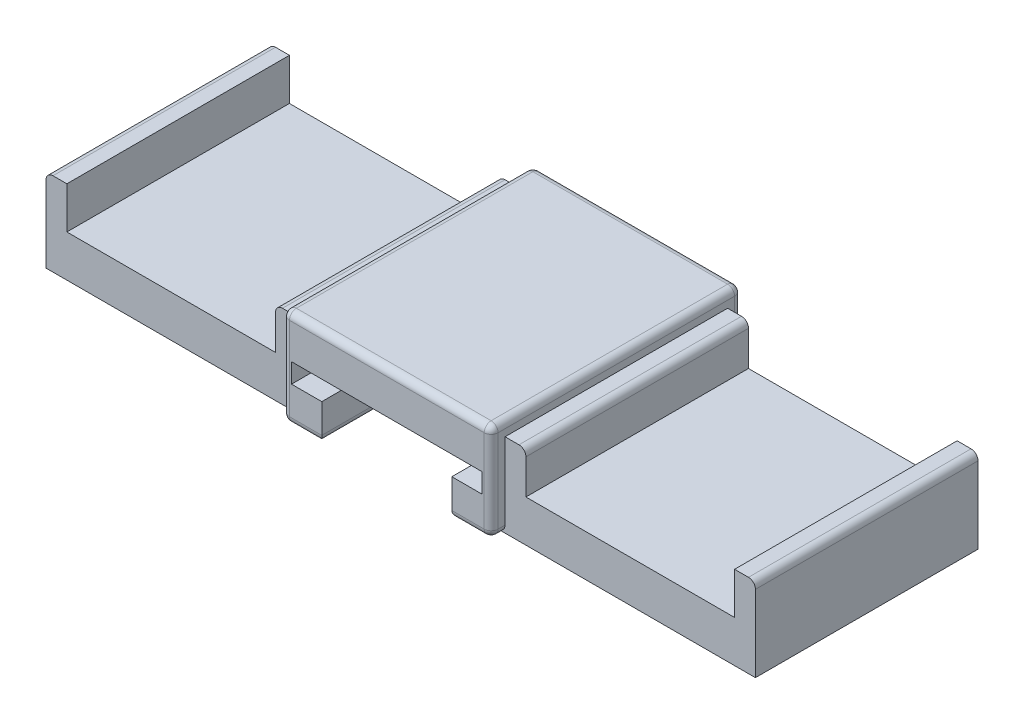
SolidWorks part; units mm, degrees
ref_plane "Front Plane" through (0, 0, 0) normal (0, 0, 1) x (1, 0, 0)
ref_plane "Top Plane" through (0, 0, 0) normal (0, 1, 0) x (1, 0, 0)
ref_plane "Right Plane" through (0, 0, 0) normal (1, 0, 0) x (0, 0, -1)
sketch "Sketch1" plane through (0, 0, 0) normal (0, 1, 0) x (1, 0, 0)
  line L1 (-7.5, -9) -> (7.5, -9)
  line L2 (-7.5, -9) -> (-7.5, 9)
  line L3 (-7.5, 9) -> (7.5, 9)
  line L4 (7.5, -9) -> (7.5, 9)
  line L5 (-7.5, -9) -> (7.5, 9) construction
  line L6 (-7.5, 9) -> (7.5, -9) construction
  point P0 (0, 0)
  dimension "D1" = 18
  dimension "D2" = 15
extrude "Boss-Extrude1" add sketch "Sketch1" along normal blind 7
sketch "Sketch2" plane through (0, 0, 9) normal (0, 0, 1) x (1, 0, 0)
  line L0 (-6.85, 0) -> (6.85, 0)
  line L1 (-7.5, 0) -> (7.5, 0) construction
  line L2 (6.85, 0) -> (6.85, 4)
  line L3 (6.85, 4) -> (-6.85, 4)
  line L4 (-6.85, 4) -> (-6.85, 0)
  line L5 (-6.85, 2.6) -> (6.85, 2.6)
  line L6 (-4.675, 2.6) -> (-4.675, 0)
  line L7 (0, 0) -> (0, 7) construction
  line L8 (-7.5, 7) -> (7.5, 7) construction
  line L9 (4.675, 2.6) -> (4.675, 0)
  line L10 (-0.6, 0) -> (-0.6, 5)
  line L11 (-0.6, 5) -> (0.6, 5)
  line L12 (0.6, 5) -> (0.6, 0)
  line L13 (1.1, 2.6) -> (1.1, 0)
  line L14 (-1.1, 2.6) -> (-1.1, 0)
  point P6 (0, 0)
  dimension "D1" = 4
  dimension "D2" = 1.4
  dimension "D3" = 9.35
  dimension "D4" = 1.2
  dimension "0.5" = 0.5
  dimension "D6" = 13.7
extrude "Cut-Extrude1" cut sketch "Sketch2" against normal blind 14.2 contours L5 L10 L3 L4 | L3 L12 L5 L2 | L14 L5 L6 L0 | L5 L13 L4 L9 | L7 L0 L12 L5 | L4 L7 L5 L10 | L5 L7 L3 L10 | L7 L5 L12 L3
sketch "Sketch8" plane through (0, 0, 9) normal (0, 0, 1) x (1, 0, 0)
  line L0 (-1.1, 2.6) -> (-0.6, 2.6)
  line L1 (-0.6, 2.6) -> (-0.6, 0)
  line L2 (-0.6, 0) -> (-1.1, 0)
  line L3 (-1.1, 0) -> (-1.1, 2.6)
  line L4 (0.6, 2.6) -> (1.1, 2.6)
  line L5 (1.1, 2.6) -> (1.1, 0)
  line L6 (1.1, 0) -> (0.6, 0)
  line L7 (0.6, 0) -> (0.6, 2.6)
extrude "Cut-Extrude4" cut sketch "Sketch8" against normal blind 10
sketch "Sketch9" plane through (-7.5, 0, 0) normal (-1, 0, 0) x (0, 0, 1)
  line L0 (-8, 0) -> (-8, 6)
  line L1 (9, 0) -> (-9, 0) construction
  line L2 (-8, 6) -> (8, 6)
  line L3 (8, 6) -> (8, 0)
  line L4 (-9, 0) -> (9, 0) construction
  line L5 (8, 0) -> (-8, 0)
  line L6 (-0.3093, 0) -> (0, 0) construction
  line L7 (0, 0) -> (0, 6) construction
  dimension "D1" = 16
  dimension "D2" = 6
extrude "Boss-Extrude2" add sketch "Sketch9" along normal blind 18
sketch "Sketch12" plane through (0, 0, 8) normal (0, 0, 1) x (1, 0, 0)
  line L0 (-16.5, 0) -> (-16.5, 6) construction
  line L1 (-25.5, 0) -> (-7.5, 0) construction
  line L2 (-25.5, 6) -> (-7.5, 6) construction
  dimension "D1" = 16.5
sketch "Sketch13" plane through (7.5, 0, 0) normal (1, 0, 0) x (0, 0, -1)
  line L0 (-8, 0) -> (-8, 6)
  line L1 (-8, 0) -> (-8, 6) construction
  line L2 (-8, 6) -> (8, 6)
  line L3 (8, 6) -> (8, 0)
  line L4 (9, 0) -> (-9, 0) construction
  line L5 (8, 0) -> (-8, 0)
  line L6 (0, 0) -> (0, 7) construction
  line L7 (-9, 0) -> (9, 0) construction
  line L8 (-9, 7) -> (9, 7) construction
  dimension "D2" = 6
extrude "Boss-Extrude3" add sketch "Sketch13" along normal blind 18
sketch "Sketch14" plane through (0, 0, 9) normal (0, 0, 1) x (1, 0, 0)
  line L0 (0, 0) -> (0, 7) construction
  line L1 (-7.5, 7) -> (7.5, 7) construction
  line L3 (25.5, 0) -> (7.5, 0) construction
  line L7 (16.5, 0) -> (16.5, 0.2814) construction
  line L12 (16.5, 0) -> (16.5, 6) construction
  line L13 (25.5, 6) -> (7.5, 6) construction
  line L17 (9, 6) -> (9, 3)
  line L18 (9, 3) -> (24, 3)
  line L19 (24, 3) -> (24, 6)
  line L20 (24, 6) -> (9, 6)
  line L23 (-24, 3) -> (-24, 6)
  line L24 (-9, 3) -> (-24, 3)
  line L25 (-9, 6) -> (-9, 3)
  line L30 (-24, 6) -> (-9, 6)
  dimension "D1" = 15
  dimension "D2" = 3
extrude "Cut-Extrude5" cut sketch "Sketch14" against normal blind 32.55
fillet "Fillet1" radius 0.5 21 edges at (0, 0, -9) (7.5, 0, -8.5) (-7.5, 0, -8.5) (-7.5, 0, 8.5) (7.5, 0, 8.5) (7.5, 7, 0) (25.5, 6, 0) (-25.5, 6, 0) (-7.5, 7, 0) (-7.5, 3.5, 9) (7.5, 3.5, 9) (6.0875, 0, 9) (4.675, 0, 1.9) (-4.675, 0, 1.9) (-6.0875, 0, 9) (0, 7, 9) (0, 7, -9) (7.5, 3.5, -9) (-7.5, 3.5, -9) (-9, 6, 0) (9, 6, 0)
